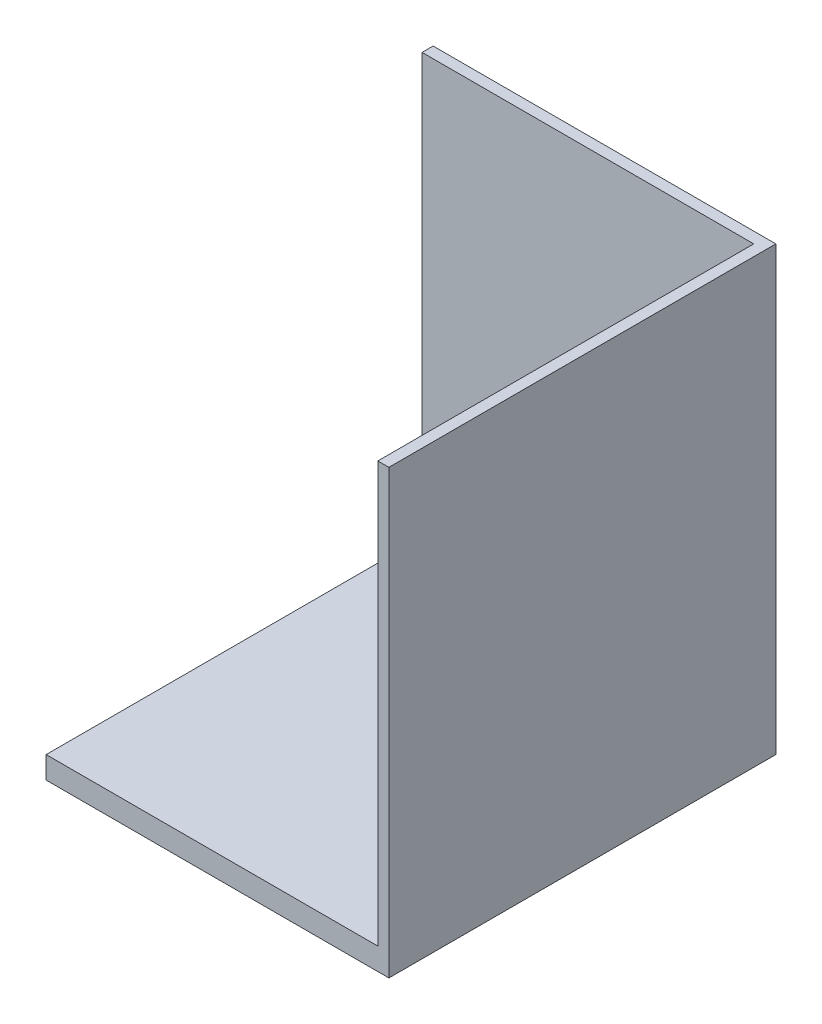
SolidWorks part; units mm, degrees
ref_plane "Front Plane" through (0, 0, 0) normal (0, 0, 1) x (1, 0, 0)
ref_plane "Top Plane" through (0, 0, 0) normal (0, 1, 0) x (1, 0, 0)
ref_plane "Right Plane" through (0, 0, 0) normal (1, 0, 0) x (0, 0, -1)
sketch "Sketch1" plane through (0, 0, 0) normal (0, 0, 1) x (1, 0, 0)
  line L0 (-84.7826, -33.2609) -> (65.2174, -33.2609)
  line L1 (65.2174, -33.2609) -> (65.2174, -43.2609)
  line L2 (65.2174, -43.2609) -> (-84.7826, -43.2609)
  line L3 (-84.7826, -43.2609) -> (-84.7826, -33.2609)
  dimension "D1" = 10
  dimension "D2" = 150
extrude "Boss-Extrude1" add sketch "Sketch1" against normal blind 200
sketch "Sketch2" plane through (0, 0, 0) normal (0, 0, 1) x (1, 0, 0)
  line L0 (65.2174, -43.2609) -> (70.2174, -43.2609)
  line L1 (70.2174, -43.2609) -> (70.2174, 256.7391)
  line L2 (70.2174, 256.7391) -> (65.2174, 256.7391)
  line L3 (65.2174, 256.7391) -> (65.2174, -33.2609)
  line L4 (65.2174, -33.2609) -> (65.2174, -43.2609)
  dimension "D1" = 5
  dimension "D2" = 300
extrude "Boss-Extrude2" add sketch "Sketch2" against normal blind 205
sketch "Sketch3" plane through (-84.7826, 0, 0) normal (-1, 0, 0) x (0, 0, 1)
  line L0 (-205, 256.7391) -> (-205, -43.2609)
  line L1 (-205, -43.2609) -> (-200, -43.2609)
  line L2 (-200, -43.2609) -> (-200, 256.7391)
  line L3 (-205, 256.7391) -> (0, 256.7391) construction
  line L4 (-200, 256.7391) -> (-205, 256.7391)
extrude "Boss-Extrude3" add sketch "Sketch3" against normal blind 150
sketch "Sketch4" plane through (0, -43.2609, 0) normal (0, -1, 0) x (1, 0, 0)
  line L8 (-84.7826, -160) -> (25.2174, -160)
  line L9 (-84.7826, -205) -> (-84.7826, 0) construction
  line L10 (25.2174, -160) -> (25.2174, -60)
  line L11 (25.2174, -60) -> (35.2174, -60)
  line L12 (35.2174, -60) -> (35.2174, -170)
  line L13 (35.2174, -170) -> (-84.7826, -170)
  line L14 (-84.7826, -170) -> (-84.7826, -160)
  line L15 (-84.7826, -205) -> (70.2174, -205) construction
  line L16 (-84.7826, 0) -> (70.2174, 0) construction
  line M10 (-84.7826, 0) -> (-84.7826, -205)
  dimension "D1" = 110
  dimension "D2" = 10
  dimension "D4" = 35
  dimension "D5" = 10
  dimension "D6" = 110
  dimension "D7" = 60
extrude "Boss-Extrude4" add sketch "Sketch4" along normal blind 30 contours L13 L12 L11 L10 L8 M10
sketch "Sketch5" plane through (65.2174, 0, 0) normal (-1, 0, 0) x (0, 0, 1)
  line L0 (-205, 256.7391) -> (-205, -43.2609) construction
  line L2 (-205, 156.7391) -> (-30, 156.7391)
  line L3 (-205, 156.7391) -> (-205, -73.2609)
  line L4 (-205, -73.2609) -> (-30, -73.2609)
  line L5 (-30, 156.7391) -> (-30, -73.2609)
  line L9 (-160, -73.2609) -> (-60, -73.2609) construction
  line L11 (-205, 256.7391) -> (0, 256.7391)
  line L12 (-205, 256.7391) -> (-205, -73.2609)
  line L13 (-205, -73.2609) -> (0, -73.2609)
  line L14 (0, 256.7391) -> (0, -73.2609)
  line L15 (-205, 256.7391) -> (0, 256.7391)
  line L16 (-205, 256.7391) -> (-205, 156.7391)
  line L17 (-205, 156.7391) -> (0, 156.7391)
  line L18 (0, 256.7391) -> (0, 156.7391)
  dimension "D1" = 175
  dimension "D2" = 230
extrude "Cut-Extrude3" cut sketch "Sketch5" against normal through all both and the other way through all contours L11 L12 L2 L0 | L17 L5 L9 L14 | L2 L17 L14 L11 L0 | L14 L9 L5 L13
